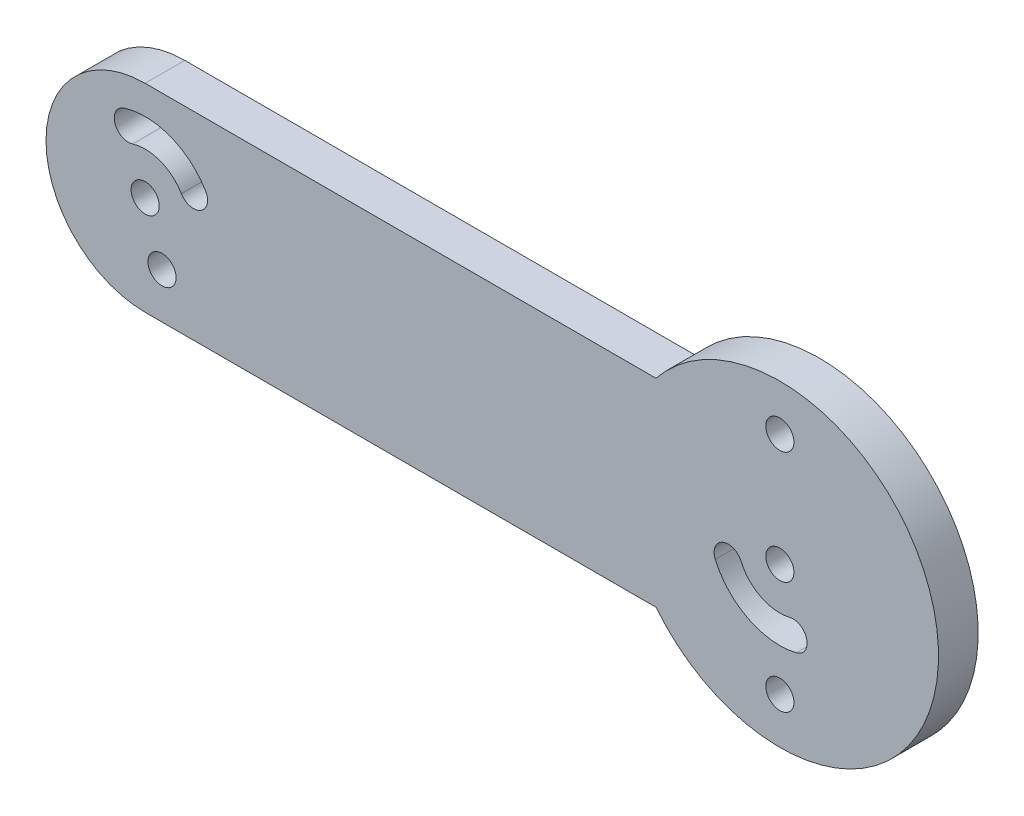
SolidWorks part; units mm, degrees
ref_plane "Front Plane" through (0, 0, 0) normal (0, 0, 1) x (1, 0, 0)
ref_plane "Top Plane" through (0, 0, 0) normal (0, 1, 0) x (1, 0, 0)
ref_plane "Right Plane" through (0, 0, 0) normal (1, 0, 0) x (0, 0, -1)
sketch "Sketch1" plane through (0, 0, 0) normal (0, 0, 1) x (1, 0, 0)
  line L0 (0.8875, 0) -> (-0.8875, 0) construction
  line L1 (-40, 6.25) -> (-7.8062, 6.25)
  line L2 (-40, -6.25) -> (-7.8062, -6.25)
  line L3 (-3.2556, -1.4156) -> (0, 0) construction
  line L4 (0, 0) -> (0.8287, -3.4519) construction
  line L5 (-40, 0) -> (-36.9539, 1.8231) construction
  line L6 (-41.0617, 3.3875) -> (-40, 0) construction
  line L7 (0, 7.1) -> (0, 0) construction
  line L8 (0.8875, 0) -> (-0.8875, 0) construction
  line L9 (-39.1125, 0) -> (-40.8875, 0) construction
  line L10 (-38.7366, 3.3176) -> (-40, 0) construction
  line L11 (-40, 0) -> (-41.2634, -3.3176) construction
  line L12 (-40, 0) -> (-38.9383, -3.3875) construction
  circle A0 centre (0, 0) radius 0.8875
  circle A1 centre (-40, 0) radius 0.8875
  arc A4 (-36.9539, 1.8231) -> (-41.0617, 3.3875) centre (-40, 0) ccw construction
  arc A5 (-36.1924, 2.2789) -> (-41.3271, 4.2344) centre (-40, 0) ccw
  arc A6 (-37.7154, 1.3674) -> (-40.7963, 2.5406) centre (-40, 0) ccw
  arc A7 (-37.7154, 1.3674) -> (-36.1924, 2.2789) centre (-36.9539, 1.8231) ccw
  arc A8 (-41.3271, 4.2344) -> (-40.7963, 2.5406) centre (-41.0617, 3.3875) ccw
  circle A9 centre (0, 7.1) radius 0.8875
  circle A10 centre (0, -7.1) radius 0.8875
  arc A11 (-7.8062, -6.25) -> (-7.8062, 6.25) centre (0, 0) ccw
  arc A12 (-40, 6.25) -> (-40, -6.25) centre (-40, 0) ccw
  arc A13 (-3.2556, -1.4156) -> (0.8287, -3.4519) centre (0, 0) ccw construction
  arc A14 (-4.0695, -1.7694) -> (1.0359, -4.3149) centre (0, 0) ccw
  arc A15 (-2.4417, -1.0617) -> (0.6215, -2.5889) centre (0, 0) ccw
  arc A16 (-2.4417, -1.0617) -> (-4.0695, -1.7694) centre (-3.2556, -1.4156) ccw
  arc A17 (1.0359, -4.3149) -> (0.6215, -2.5889) centre (0.8287, -3.4519) ccw
  circle A18 centre (-41.2634, -3.3176) radius 0.8875 construction
  circle A19 centre (-38.9383, -3.3875) radius 0.8875
  point P7 (-1.584, -3.177)
  point P15 (-38.7366, 3.3176)
  point P28 (0, 0)
  dimension "D1" = 1.775
  dimension "D6" = 20
  dimension "D4" = 12.5
  dimension "D9" = 7.1
  dimension "D3" = 40
  dimension "D8" = 90
  dimension "D10" = 76.5
  dimension "D11" = 80
  dimension "D7" = 72.599
  dimension "D5" = 3.55
  dimension "D12" = 76.5
  dimension "D2" = 2
extrude "Boss-Extrude1" add sketch "Sketch1" along normal blind 2.5
equation "\"filamentDia\"=1.775"
equation "\"D1@Sketch1\"=\"filamentDia\""
